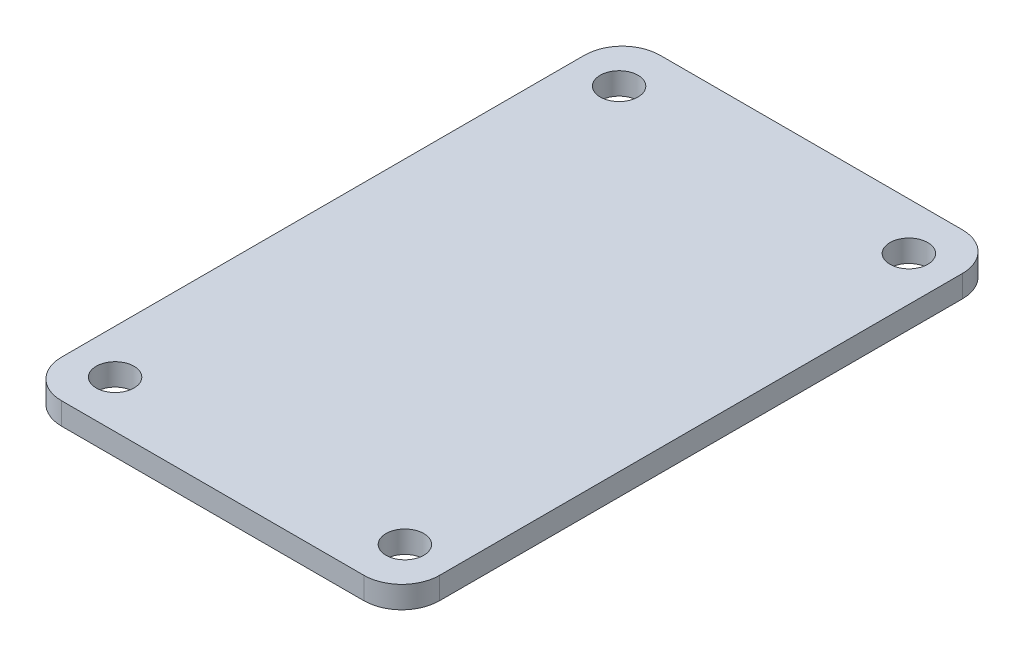
SolidWorks part; units mm, degrees
ref_plane "Ön Düzlem" through (0, 0, 0) normal (0, 0, 1) x (1, 0, 0)
ref_plane "Üst Düzlem" through (0, 0, 0) normal (0, 1, 0) x (1, 0, 0)
ref_plane "Sağ Düzlem" through (0, 0, 0) normal (1, 0, 0) x (0, 0, -1)
sketch "Sketch1" plane through (0, 0, 0) normal (0, 1, 0) x (1, 0, 0)
  line L1 (-12, -23.75) -> (12, -23.75)
  line L2 (-15, -20.75) -> (-15, 20.75)
  line L3 (-12, 23.75) -> (12, 23.75)
  line L4 (15, -20.75) -> (15, 20.75)
  line L5 (-15, -23.75) -> (15, 23.75) construction
  line L6 (-15, 23.75) -> (15, -23.75) construction
  line L7 (-11.5, -20) -> (11.5, -20) construction
  line L8 (-11.5, -20) -> (-11.5, 20) construction
  line L9 (-11.5, 20) -> (11.5, 20) construction
  line L10 (11.5, -20) -> (11.5, 20) construction
  line L11 (-11.5, -20) -> (11.5, 20) construction
  line L12 (-11.5, 20) -> (11.5, -20) construction
  circle A0 centre (-11.5, 20) radius 1.5
  circle A1 centre (11.5, 20) radius 1.5
  circle A2 centre (11.5, -20) radius 1.5
  circle A3 centre (-11.5, -20) radius 1.5
  arc A4 (-15, -20.75) -> (-12, -23.75) centre (-12, -20.75) ccw
  arc A5 (12, -23.75) -> (15, -20.75) centre (12, -20.75) ccw
  arc A6 (15, 20.75) -> (12, 23.75) centre (12, 20.75) ccw
  arc A7 (-12, 23.75) -> (-15, 20.75) centre (-12, 20.75) ccw
  point P0 (0, 0)
  point P6 (0, 0)
  dimension "D3" = 3
  dimension "D6" = 3
  dimension "D1" = 30
  dimension "D2" = 47.5
  dimension "D4" = 23
  dimension "D5" = 40
extrude "Boss-Extrude1" add sketch "Sketch1" along normal blind 1.75
